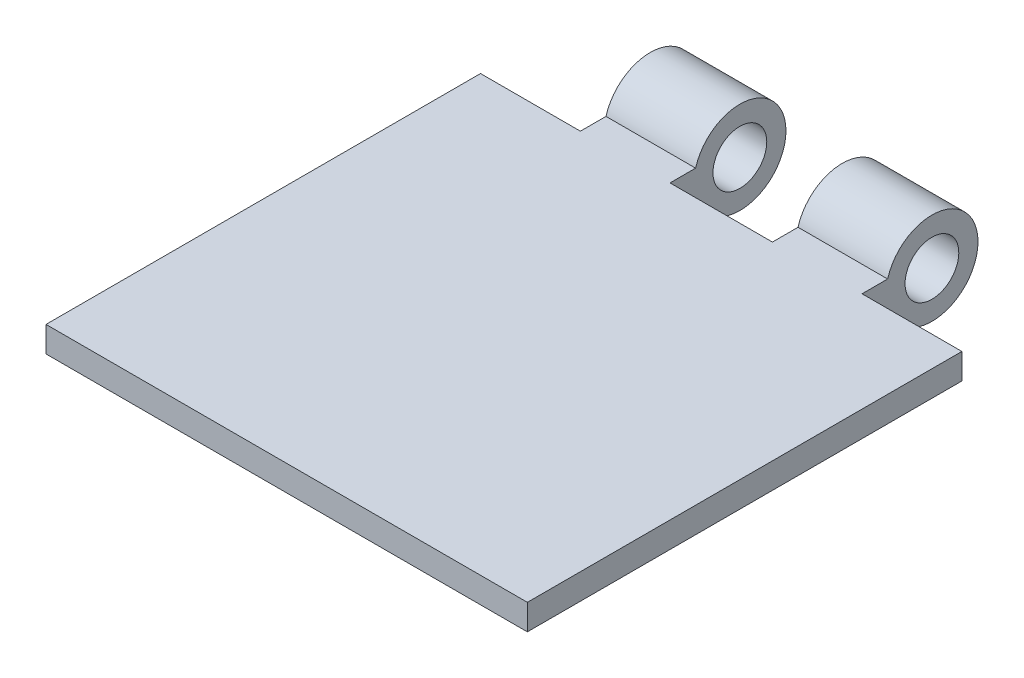
SolidWorks part; units mm, degrees
ref_plane "Front Plane" through (0, 0, 0) normal (0, 0, 1) x (1, 0, 0)
ref_plane "Top Plane" through (0, 0, 0) normal (0, 1, 0) x (1, 0, 0)
ref_plane "Right Plane" through (0, 0, 0) normal (1, 0, 0) x (0, 0, -1)
sketch "Sketch1" plane through (0, 0, 0) normal (0, 1, 0) x (1, 0, 0)
  line L1 (-23.876, 20.32) -> (23.876, 20.32)
  line L2 (-23.876, 20.32) -> (-23.876, -20.32)
  line L3 (-23.876, -20.32) -> (23.876, -20.32)
  line L4 (23.876, 20.32) -> (23.876, -20.32)
  dimension "D1" = 40.64
  dimension "D2" = 47.752
  dimension "D3" = 23.876
  dimension "D4" = 20.32
extrude "Boss-Extrude1" add sketch "Sketch1" along normal blind 2.54
sketch "Sketch3" plane through (0, 0, 0) normal (1, 0, 0) x (0, 0, -1)
  circle A0 centre (24.638, 1.27) radius 4.572
extrude "Boss-Extrude3" add sketch "Sketch3" along normal mid plane 47.752
ref_plane "Plane1" through (0, 0, -20.2459) normal (0, 0, -1) x (-1, 0, 0)
sketch "Sketch7" plane through (0, 0, -20.2459) normal (0, 0, -1) x (-1, 0, 0)
  line L15 (5.08, 7.3247) -> (-5.08, 7.3247)
  line L16 (5.08, 7.3247) -> (5.08, -5.9494)
  line L17 (5.08, -5.9494) -> (-5.08, -5.9494)
  line L18 (-5.08, 7.3247) -> (-5.08, -5.9494)
  line L19 (13.97, 6.9469) -> (24.9238, 6.9469)
  line L20 (13.97, 6.9469) -> (13.97, -5.9494)
  line L21 (13.97, -5.9494) -> (24.9238, -5.9494)
  line L22 (24.9238, 6.9469) -> (24.9238, -5.9494)
  line L23 (-13.97, 7.3247) -> (-25.3016, 7.3247)
  line L24 (-13.97, 7.3247) -> (-13.97, -5.9494)
  line L25 (-13.97, -5.9494) -> (-25.3016, -5.9494)
  line L26 (-25.3016, 7.3247) -> (-25.3016, -5.9494)
extrude "Cut-Extrude4" cut sketch "Sketch7" along normal blind 47.752 and the other way blind 2.54
sketch "Sketch8" plane through (0, 0, 20.32) normal (0, 0, 1) x (1, 0, 0)
  line L1 (-23.876, 2.54) -> (23.876, 2.54)
  line L2 (-23.876, 2.54) -> (-23.876, 0)
  line L3 (-23.876, 0) -> (23.876, 0)
  line L4 (23.876, 2.54) -> (23.876, 0)
extrude "Boss-Extrude4" add sketch "Sketch8" along normal blind 5.08
sketch "Sketch9" plane through (13.97, 0, 0) normal (1, 0, 0) x (0, 0, -1)
  circle A0 centre (24.638, 1.27) radius 2.667
  dimension "D1" = 5.334
extrude "Cut-Extrude5" cut sketch "Sketch9" against normal blind 33.782
